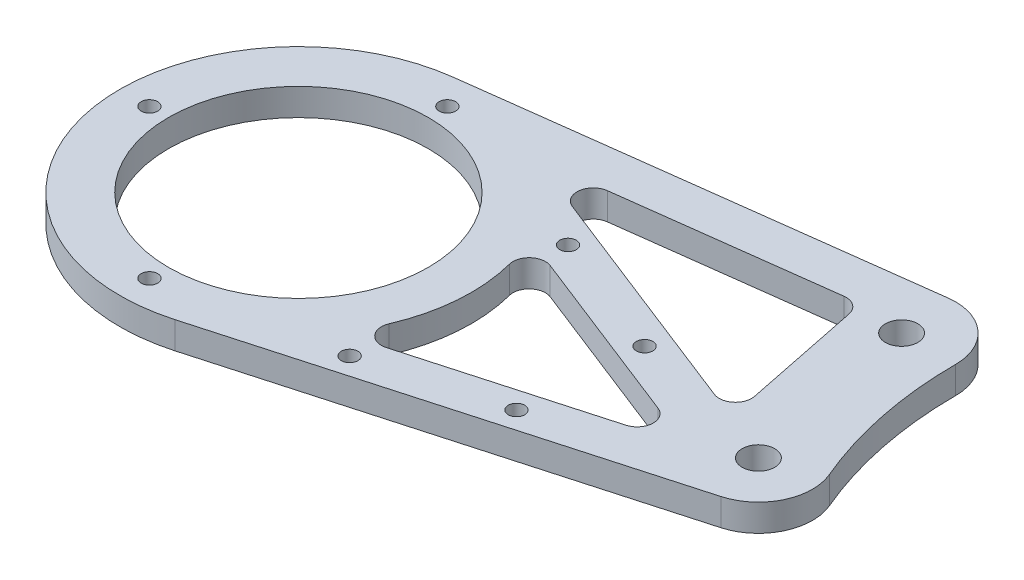
SolidWorks part; units mm, degrees
material "Thornel Mat VMA"
ref_plane "前视基准面" through (0, 0, 0) normal (0, 0, 1) x (1, 0, 0)
ref_plane "上视基准面" through (0, 0, 0) normal (0, 1, 0) x (1, 0, 0)
ref_plane "右视基准面" through (0, 0, 0) normal (1, 0, 0) x (0, 0, -1)
other "Configuration Table"
sketch "草图1" plane through (0, 0, 0) normal (0, 1, 0) x (1, 0, 0)
  line L0 (0, 0) -> (85, 0) construction
  line L1 (0, 0) -> (78.2429, 33.2121) construction
  line L2 (8.9294, -31.7689) -> (87.7059, -9.627)
  line L3 (-4.1935, 32.7325) -> (76.9721, 43.1311)
  circle A0 centre (0, 0) radius 13.1
  circle A1 centre (0, 0) radius 17.5 construction
  circle A2 centre (0, 17.5) radius 2.025
  circle A3 centre (8.75, 15.1554) radius 2.025
  circle A4 centre (15.1554, 8.75) radius 2.025
  circle A5 centre (17.5, 0) radius 2.025
  circle A6 centre (15.1554, -8.75) radius 2.025
  circle A7 centre (8.75, -15.1554) radius 2.025
  circle A8 centre (0, -17.5) radius 2.025
  circle A9 centre (-8.75, -15.1554) radius 2.025
  circle A10 centre (-15.1554, -8.75) radius 2.025
  circle A11 centre (-17.5, 0) radius 2.025
  circle A12 centre (-15.1554, 8.75) radius 2.025
  circle A13 centre (-8.75, 15.1554) radius 2.025
  circle A14 centre (0, 0) radius 33
  circle A15 centre (85, 0) radius 3
  circle A16 centre (78.2429, 33.2121) radius 3
  circle A17 centre (78.2429, 33.2121) radius 10
  circle A18 centre (85, 0) radius 10
  circle A19 centre (163.2429, 33.2121) radius 75
  point P31 (0, 0)
  dimension "D1" = 26.2
  dimension "D2" = 35
  dimension "D3" = 4.05
  dimension "D5" = 66
  dimension "D6" = 6
  dimension "D9" = 20
  dimension "D10" = 150
  dimension "D7" = 85
  dimension "D8" = 23
  dimension "D4" = 12
extrude "凸台-拉伸1" add sketch "草图1" along normal blind 5 contours A19 A17 L3 A14 L2 A18 | A14 A0 A2 A3 A4 A5 A6 A7 A8 A9 A10 A11 A12 A13 | A18 A15 | A17 A16
sketch "草图3" plane through (0, 5, 0) normal (0, 1, 0) x (1, 0, 0)
  circle A0 centre (0, 0) radius 24
  dimension "D1" = 48
extrude "切除-拉伸2" cut sketch "草图3" against normal blind 10
sketch "草图4" plane through (0, 5, 0) normal (0, 1, 0) x (1, 0, 0)
  line L0 (25.9945, -18.6624) -> (76.1087, -4.5766)
  line L1 (8.9294, -31.7689) -> (87.7059, -9.627) construction
  line L2 (28.7852, 13.979) -> (76.1087, -4.5766)
  line L3 (75.8816, 4.1055) -> (16.6361, 27.3357)
  line L4 (16.6361, 27.3357) -> (69.7704, 34.143)
  line L5 (-4.1935, 32.7325) -> (76.9721, 43.1311) construction
  line L6 (69.7704, 34.143) -> (75.8816, 4.1055)
  line L7 (78.2429, 33.2121) -> (85, 0) construction
  circle A0 centre (0, 0) radius 32
  circle A1 centre (85, 0) radius 10
  dimension "D1" = 64
  dimension "D2" = 20
  dimension "D3" = 8
  dimension "D4" = 8
  dimension "D5" = 8
extrude "切除-拉伸3" cut sketch "草图4" against normal blind 10 contours L6 L4 L3 | A0 L0 L2
fillet "圆角1" radius 3 6 edges at (28.7852, 2.5, -13.979) (76.1087, 2.5, 4.5766) (25.9945, 2.5, 18.6624) (16.6361, 2.5, -27.3357) (69.7704, 2.5, -34.143) (75.8816, 2.5, -4.1055)
sketch "草图7" plane through (0, 0, 0) normal (0, -1, 0) x (1, 0, 0)
  circle A0 centre (0, -27.5222) radius 1.525 construction
  circle A1 centre (33.3215, -16.4968) radius 1.525 construction
  circle A2 centre (-27.5222, 0) radius 1.525 construction
  circle A3 centre (0, 27.5222) radius 1.525 construction
  circle A4 centre (30.9017, 21.4381) radius 1.525 construction
  circle A5 centre (56.5963, -7.3707) radius 1.525 construction
  circle A6 centre (54.9691, 14.6734) radius 1.525 construction
  circle A7 centre (0, -27.5222) radius 1.525
  circle A8 centre (33.3215, -16.4968) radius 1.525
  circle A9 centre (-27.5222, 0) radius 1.525
  circle A10 centre (0, 27.5222) radius 1.525
  circle A11 centre (30.9017, 21.4381) radius 1.525
  circle A12 centre (56.5963, -7.3707) radius 1.525
  circle A13 centre (54.9691, 14.6734) radius 1.525
extrude "切除-拉伸4" cut sketch "草图7" against normal blind 10
